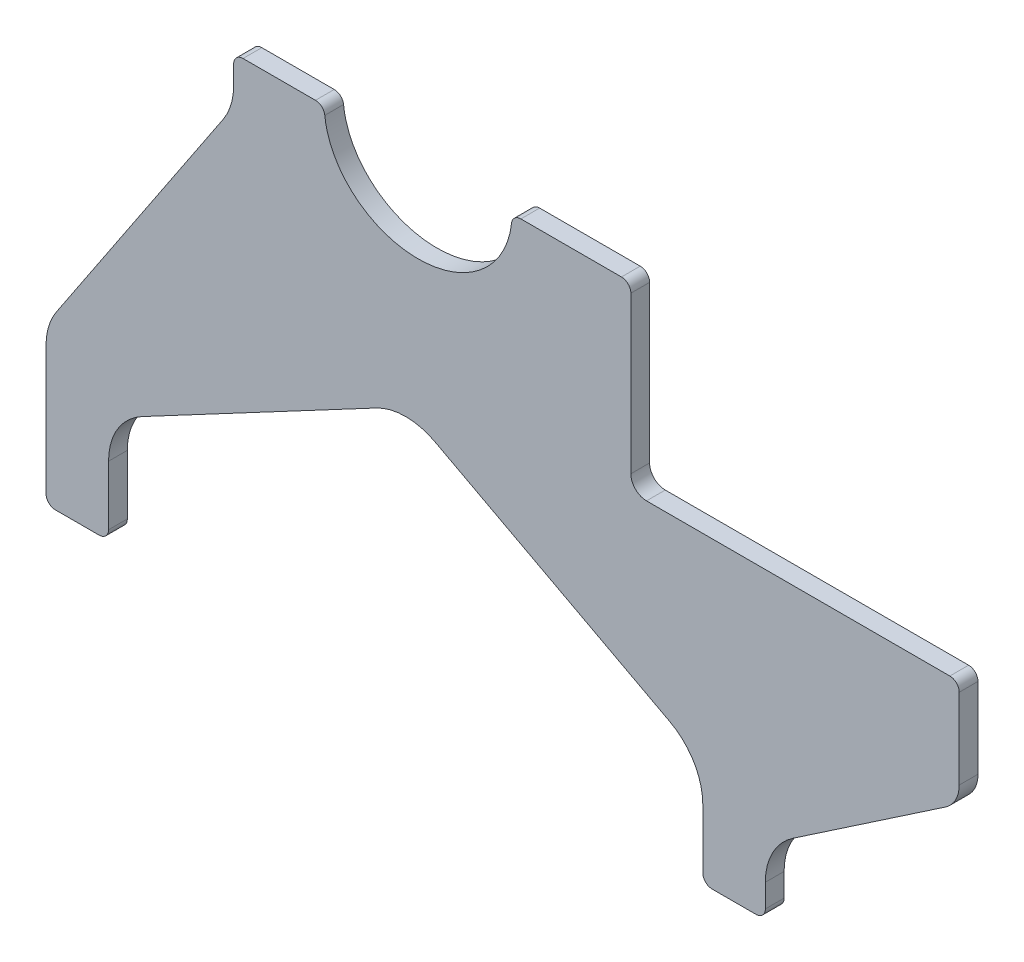
SolidWorks part; units mm, degrees
ref_plane "Plane1" through (0, 0, 0) normal (0, 0, 1) x (1, 0, 0)
ref_plane "Plane2" through (0, 0, 0) normal (0, 1, 0) x (1, 0, 0)
ref_plane "Plane3" through (0, 0, 0) normal (1, 0, 0) x (0, 0, -1)
sketch "Sketch1" plane through (0, 0, 0) normal (0, 0, 1) x (1, 0, 0)
  line L0 (-9.3894, -4.9924) -> (-84.3894, -44.8707)
  line L1 (-95, -62.5296) -> (-95, -81.5124)
  line L2 (-98, -84.5124) -> (-112, -84.5124)
  line L3 (-115, -81.5124) -> (-115, -40.5679)
  line L4 (-111.641, -29.4739) -> (-58.359, 50.4491)
  line L5 (77, 12.4876) -> (174, 12.4876)
  line L6 (-55, 67.4876) -> (-55, 61.5431)
  line L7 (177, 9.4876) -> (177, -16.2081)
  line L8 (98, -84.5124) -> (112, -84.5124)
  line L9 (84.3894, -44.8707) -> (9.3894, -4.9924)
  line L10 (0, 0) -> (0, -28.3157) construction
  line L12 (-52, 70.4876) -> (-28.8401, 70.4876)
  line L13 (72, 17.4876) -> (72, 67.4876)
  line L14 (172.6085, -24.4873) -> (123.783, -57.5626)
  line L15 (36.8401, 70.4876) -> (69, 70.4876)
  line L16 (95, -62.5296) -> (95, -81.5124)
  line L17 (115, -81.5124) -> (115, -74.121)
  arc A0 (112, -84.5124) -> (115, -81.5124) centre (112, -81.5124) ccw
  arc A1 (-9.3894, -4.9924) -> (9.3894, -4.9924) centre (0, -22.6514) cw
  arc A2 (-84.3894, -44.8707) -> (-95, -62.5296) centre (-75, -62.5296) ccw
  arc A3 (69, 70.4876) -> (72, 67.4876) centre (69, 67.4876) cw
  arc A4 (95, -81.5124) -> (98, -84.5124) centre (98, -81.5124) ccw
  arc A5 (84.3894, -44.8707) -> (95, -62.5296) centre (75, -62.5296) cw
  arc A6 (-95, -81.5124) -> (-98, -84.5124) centre (-98, -81.5124) cw
  arc A7 (-112, -84.5124) -> (-115, -81.5124) centre (-112, -81.5124) cw
  arc A8 (72, 17.4876) -> (77, 12.4876) centre (77, 17.4876) ccw
  arc A9 (115, -74.121) -> (123.783, -57.5626) centre (135, -74.121) cw
  arc A10 (-115, -40.5679) -> (-111.641, -29.4739) centre (-95, -40.5679) cw
  arc A11 (177, -16.2081) -> (172.6085, -24.4873) centre (167, -16.2081) cw
  arc A12 (-55, 61.5431) -> (-58.359, 50.4491) centre (-75, 61.5431) cw
  arc A13 (-25.8571, 67.8064) -> (-28.8401, 70.4876) centre (-28.8401, 67.4876) ccw
  arc A14 (33.8571, 67.8064) -> (36.8401, 70.4876) centre (36.8401, 67.4876) cw
  arc A15 (-55, 67.4876) -> (-52, 70.4876) centre (-52, 67.4876) cw
  arc A16 (174, 12.4876) -> (177, 9.4876) centre (174, 9.4876) cw
  ellipse E0 centre (4, 70.4876) end of major axis (34, 70.4876) minor radius 27.5 (33.8571, 67.8064) -> (-25.8571, 67.8064) cw
  point P22 (-95, -50.5124)
  point P26 (72, 70.4876)
  point P34 (-95, -84.5124)
  point P37 (-115, -84.5124)
  point P49 (115, -63.5124)
  point P52 (-115, -34.5124)
  point P55 (177, -21.5124)
  point P58 (-55, 55.4876)
  point P67 (177, 12.4876)
  dimension "D19" = 21
  dimension "D20" = 20
  dimension "D4" = 72
  dimension "D21" = 5
  dimension "D22" = 20
  dimension "D23" = 20
  dimension "D28" = 3
  dimension "D16" = 60
  dimension "D15" = 3
  dimension "D12" = 20
  dimension "D6" = 3
  dimension "D25" = 10
  dimension "D26" = 20
  dimension "D29" = 3
  dimension "D1" = 62
  dimension "D2" = 62
  dimension "D3" = 95
  dimension "D5" = 20
  dimension "D7" = 34
  dimension "D9" = 155
  dimension "D10" = 15
  dimension "D11" = 105
  dimension "D13" = 50
  dimension "D14" = 97
  dimension "D17" = 34
  dimension "D18" = 68
  dimension "D24" = 27.5
  dimension "D27" = 60
extrude "Extrude1" add sketch "Sketch1" along normal blind 6
